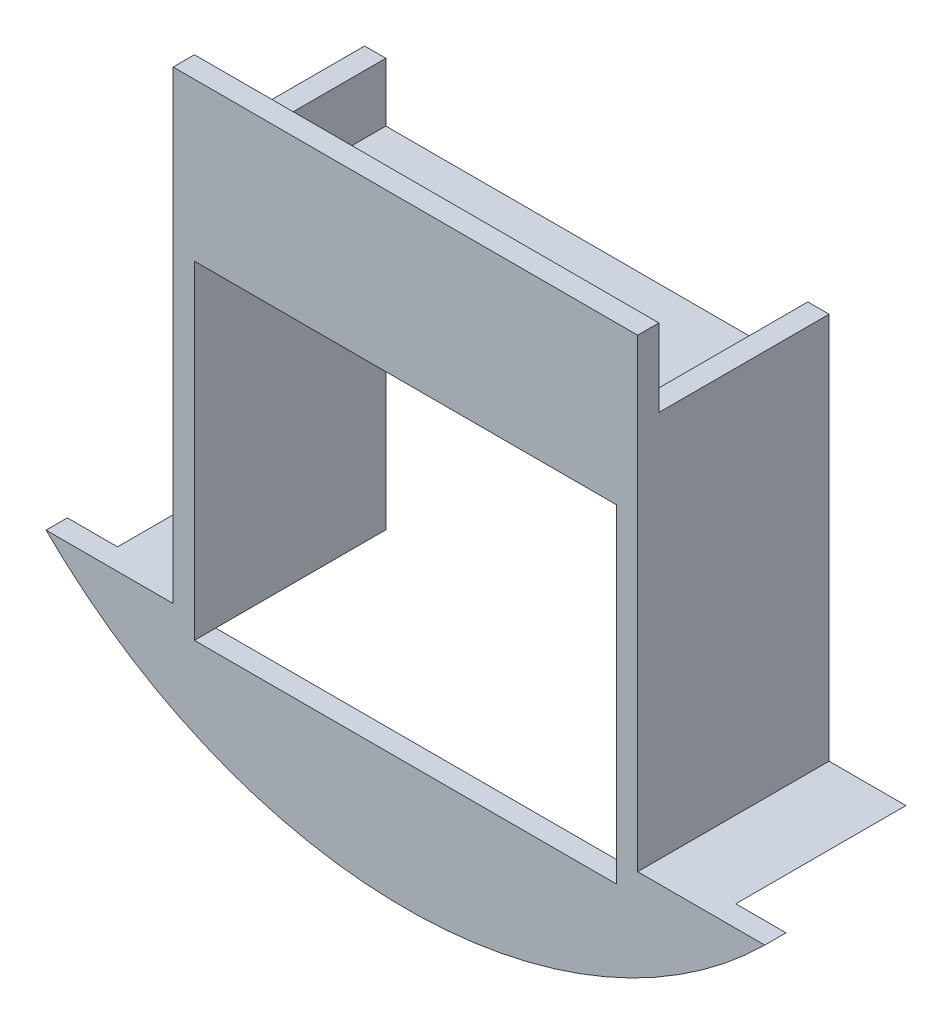
SolidWorks part; units mm, degrees
ref_plane "Front Plane" through (0, 0, 0) normal (0, 0, 1) x (1, 0, 0)
ref_plane "Top Plane" through (0, 0, 0) normal (0, 1, 0) x (1, 0, 0)
ref_plane "Right Plane" through (0, 0, 0) normal (1, 0, 0) x (0, 0, -1)
sketch "Sketch2" plane through (0, 0, 0) normal (0, 0, 1) x (1, 0, 0)
  line L0 (-34.671, -49.022) -> (-31.496, -49.022)
  line L1 (-31.496, -49.022) -> (-31.496, 0)
  line L2 (-31.496, 0) -> (31.496, 0)
  line L3 (31.496, 0) -> (31.496, -49.022)
  line L4 (31.496, -49.022) -> (34.671, -49.022)
  line L5 (34.671, -49.022) -> (34.671, 11.938)
  line L6 (34.671, 11.938) -> (31.496, 11.938)
  line L7 (31.496, 11.938) -> (31.496, 3.175)
  line L8 (31.496, 3.175) -> (-31.496, 3.175)
  line L9 (-31.496, 3.175) -> (-31.496, 11.938)
  line L10 (-31.496, 11.938) -> (-34.671, 11.938)
  line L11 (-34.671, 11.938) -> (-34.671, -49.022)
  line L12 (-31.496, 0) -> (-31.496, 3.175) construction
  point P13 (0, 0)
  dimension "D1" = 60.96
  dimension "D2" = 3.175
  dimension "D3" = 62.992
  dimension "D4" = 49.022
extrude "Boss-Extrude2" add sketch "Sketch2" along normal blind 25.4
sketch "Sketch4" plane through (0, 0, 25.4) normal (0, 0, 1) x (1, 0, 0)
  line L0 (-34.671, -49.022) -> (-42.1386, -49.022)
  line L1 (-46.1453, -45.847) -> (-34.671, -45.847)
  line L3 (-34.671, -45.847) -> (-34.671, -49.022)
  line L4 (0, 0) -> (0, 8.2702) construction
  line L5 (34.671, -45.847) -> (34.671, -49.022)
  line L6 (46.1453, -45.847) -> (34.671, -45.847)
  line L7 (34.671, -49.022) -> (42.1386, -49.022)
  arc A0 (-42.1386, -49.022) -> (-46.1453, -45.847) centre (0, 8.2702) cw
  arc A1 (42.1386, -49.022) -> (46.1453, -45.847) centre (0, 8.2702) ccw
  dimension "D1" = 71.12
  dimension "D2" = 3.175
  dimension "D3" = 42.1386
extrude "Boss-Extrude4" add sketch "Sketch4" against normal up to surface (25.4 mm away) up to face at (0, -11.8322, 0)
sketch "Sketch5" plane through (0, 0, 25.4) normal (0, 0, 1) x (1, 0, 0)
  line L0 (-34.671, 11.938) -> (-34.671, -45.847) construction
  line L2 (-34.671, -45.847) -> (-34.671, 23.5102)
  line L3 (-34.671, 23.5102) -> (34.671, 23.5102)
  line L4 (34.671, -45.847) -> (34.671, 23.5102)
  line L5 (34.671, -45.847) -> (34.671, 11.938) construction
  line L16 (-53.6449, -45.847) -> (-34.671, -45.847)
  line L17 (34.671, -45.847) -> (53.6449, -45.847)
  line L19 (-31.496, 0) -> (31.496, 0)
  line L20 (-31.496, 0) -> (-31.496, -49.022)
  line L21 (-31.496, -49.022) -> (31.496, -49.022)
  line L22 (31.496, 0) -> (31.496, -49.022)
  arc A0 (-53.6449, -45.847) -> (53.6449, -45.847) centre (0, 8.2702) ccw
  arc A1 (-46.1453, -45.847) -> (-42.1386, -49.022) centre (0, 8.2702) ccw construction
  point P12 (0, -67.9298)
  dimension "D1" = 76.2
  dimension "D2" = 91.44
extrude "Boss-Extrude5" add sketch "Sketch5" along normal blind 3.175
